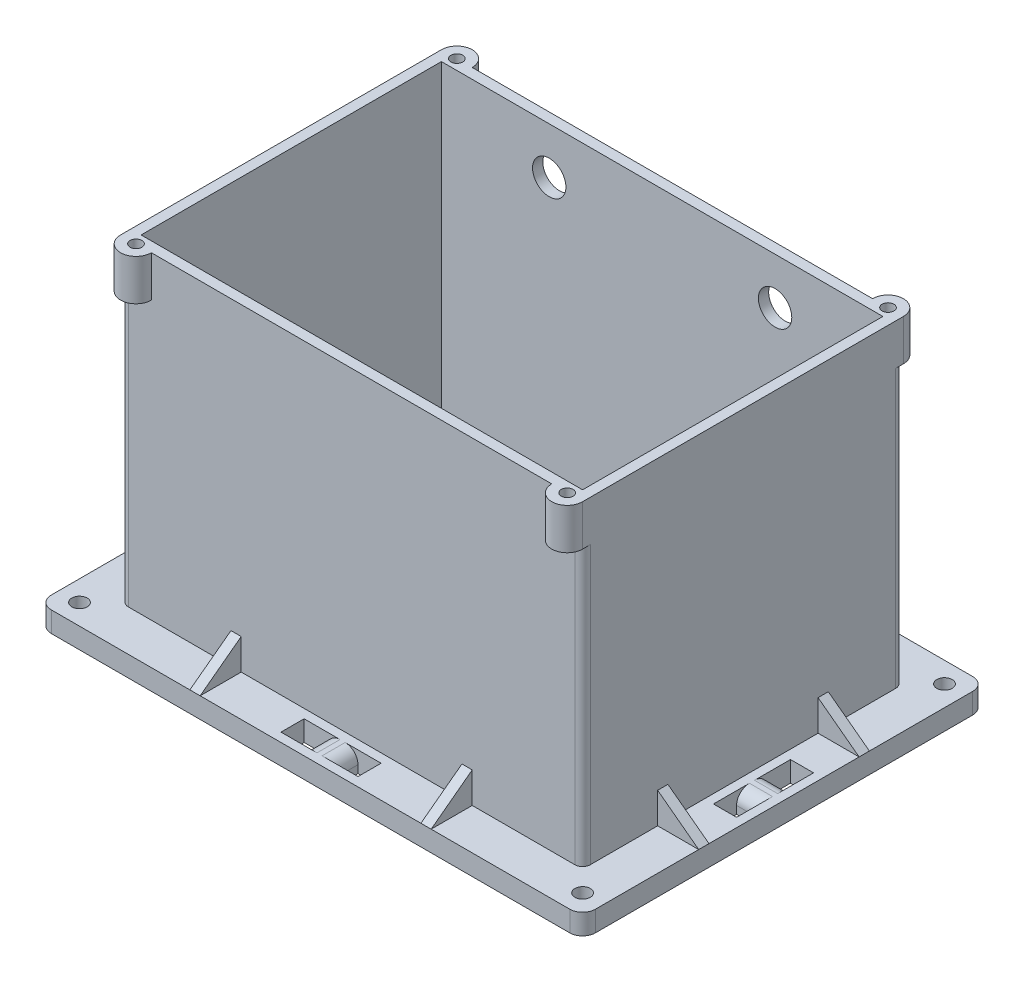
SolidWorks part; units mm, degrees
material "ABS"
ref_plane "Front Plane" through (0, 0, 0) normal (0, 0, 1) x (1, 0, 0)
ref_plane "Top Plane" through (0, 0, 0) normal (0, 1, 0) x (1, 0, 0)
ref_plane "Right Plane" through (0, 0, 0) normal (1, 0, 0) x (0, 0, -1)
sketch "Base" plane through (0, 0, 0) normal (0, 1, 0) x (1, 0, 0)
  line L1 (0, 0) -> (90, 0)
  line L2 (0, 0) -> (0, 62.5)
  line L3 (0, 62.5) -> (90, 62.5)
  line L4 (90, 0) -> (90, 62.5)
  dimension "D1" = 62.5
  dimension "D2" = 90
extrude "Base Extrude" add sketch "Base" along normal blind 2
sketch "Walls" plane through (0, 2, 0) normal (0, 1, 0) x (1, 0, 0)
  line L0 (0, 62.5) -> (0, 0) construction
  line L1 (2, 2) -> (88, 2)
  line L2 (2, 2) -> (2, 60.5)
  line L3 (2, 60.5) -> (88, 60.5)
  line L4 (88, 2) -> (88, 60.5)
  line L5 (90, 62.5) -> (0, 62.5) construction
  dimension "D1" = 86
  dimension "D2" = 58.5
  dimension "D3" = 2
  dimension "D4" = 2
extrude "Walls Extrude" add sketch "Walls" along normal blind 64 thin
sketch "Outjut" plane through (0, 66, 0) normal (0, 1, 0) x (1, 0, 0)
  line L0 (0, 0) -> (0, 62.5) construction
  line L1 (0, 62.5) -> (6, 62.5)
  line L2 (90, 62.5) -> (84, 62.5)
  line L3 (45, 64) -> (45, 0) construction
  line L4 (0, 0) -> (90, 0) construction
  line L5 (0, 31.25) -> (92, 31.25) construction
  line L6 (90, 0) -> (84, 0)
  line L7 (0, 0) -> (6, 0)
  arc A0 (0, 62.5) -> (6, 62.5) centre (3, 62.5) cw
  arc A1 (90, 62.5) -> (84, 62.5) centre (87, 62.5) ccw
  arc A2 (90, 0) -> (84, 0) centre (87, 0) cw
  arc A3 (0, 0) -> (6, 0) centre (3, 0) ccw
  point P4 (3, 65.5)
  dimension "D1" = 6
  dimension "D2" = 3
extrude "Outjut Extrude" add sketch "Outjut" against normal blind 8
sketch "Holes" plane through (0, 66, 0) normal (0, 1, 0) x (1, 0, 0)
  line L0 (45, 62.5) -> (45, 0) construction
  line L2 (84, 62.5) -> (6, 62.5) construction
  line L3 (6, 0) -> (84, 0) construction
  line L4 (90, 31.25) -> (0, 31.25) construction
  line L5 (90, 0) -> (90, 62.5) construction
  line L6 (0, 62.5) -> (0, 0) construction
  circle A1 centre (3, 62.5) radius 1.15
  circle A2 centre (87, 62.5) radius 1.15
  circle A3 centre (87, 0) radius 1.15
  circle A4 centre (3, 0) radius 1.15
  dimension "D1" = 2.3
extrude "Holes Cut" cut sketch "Holes" against normal blind 6
sketch "Switch Hole" plane through (0, 0, 0) normal (0, 0, 1) x (1, 0, 0)
  line L0 (90, 58) -> (90, 0) construction
  line L2 (0, 0) -> (90, 0) construction
  line L5 (74, 23) -> (85, 23)
  line L6 (74, 23) -> (74, 28)
  line L7 (74, 28) -> (85, 28)
  line L8 (85, 23) -> (85, 28)
  dimension "D1" = 11
  dimension "D2" = 5
  dimension "D3" = 5
  dimension "D4" = 23
extrude "Switch Hole Cut" [suppressed] cut sketch "Switch Hole" against normal up to surface (2 mm away)
sketch "Antenna/GPS Holes" plane through (0, 0, -62.5) normal (0, 0, -1) x (-1, 0, 0)
  line L0 (-90, 0) -> (0, 0) construction
  line L1 (0, 58) -> (0, 0) construction
  line L2 (-45, 66) -> (-45, 0) construction
  line L3 (-84, 66) -> (-6, 66) construction
  circle A0 centre (-23, 56.95) radius 3.25
  circle A2 centre (-67, 56.95) radius 3.25
  dimension "D1" = 6.5
  dimension "D2" = 56.95
  dimension "D3" = 23
extrude "Antenna/GPS Holes Cut" cut sketch "Antenna/GPS Holes" against normal up to surface (2 mm away) up to face at (45, 34, -60.5)
sketch "Pad" plane through (0, 0, 0) normal (0, -1, 0) x (1, 0, 0)
  line L2 (0, 0) -> (0, -62.5)
  line L4 (-8, 8) -> (-8, -70.5)
  line L5 (0, 0) -> (90, 0)
  line L7 (-8, 8) -> (98, 8)
  line L9 (90, -62.5) -> (0, -62.5)
  line L11 (98, -70.5) -> (-8, -70.5)
  line L14 (90, -62.5) -> (90, 0)
  line L16 (98, -70.5) -> (98, 8)
  dimension "D2" = 8
  dimension "D1" = 8
  dimension "D3" = 8
  dimension "D4" = 8
extrude "Pad Extrude" add sketch "Pad" against normal blind 4 contours L7 L16 L11 L4
sketch "Screw Holes" plane through (0, 4, 0) normal (0, 1, 0) x (1, 0, 0)
  line L0 (98, 70.5) -> (90, 62.5) construction
  line L1 (45, 70.5) -> (45, -8) construction
  line L2 (98, 70.5) -> (-8, 70.5) construction
  line L3 (-8, -8) -> (98, -8) construction
  line L4 (-8, 31.25) -> (98, 31.25) construction
  line L5 (-8, -8) -> (-8, 70.5) construction
  line L6 (98, 70.5) -> (98, -8) construction
  circle A0 centre (94, 66.5) radius 1.5
  circle A1 centre (-4, 66.5) radius 1.5
  circle A2 centre (94, -4) radius 1.5
  circle A3 centre (-4, -4) radius 1.5
  dimension "D1" = 3
extrude "Screw Holes Cut" cut sketch "Screw Holes" against normal through all
fillet "Wall Fillets" radius 1.5 4 edges at (90, 31, -62.5) (90, 31, 0) (0, 31, 0) (0, 31, -62.5)
ref_plane "Length Support Plane" through (22.5, 0, 0) normal (1, 0, 0) x (0, 0, -1)
ref_plane "Length Center Plane" through (45, 0, 0) normal (1, 0, 0) x (0, 0, -1)
ref_plane "Width Support Plane" through (0, 0, -15.625) normal (0, 0, 1) x (1, 0, 0)
ref_plane "Width Center Plane" through (0, 0, -31.25) normal (0, 0, 1) x (1, 0, 0)
sketch "Length Supports" plane through (22.5, 0, 0) normal (1, 0, 0) x (0, 0, -1)
  line L0 (0, 4) -> (-8, 4)
  line L1 (-8, 4) -> (0, 10)
  line L2 (0, 4) -> (0, 58) construction
  line L3 (0, 10) -> (0, 4)
  dimension "D1" = 6
extrude "Length Supports Extrude" add sketch "Length Supports" along normal blind 1 and the other way blind 1
mirror "Length Support Extrude Mirror" about plane through (45, 0, 0) normal (1, 0, 0) of "Length Supports Extrude"
mirror "Length Support Extrude Opposing Mirror" about plane through (0, 0, -31.25) normal (0, 0, 1) of "Length Supports Extrude", "Length Support Extrude Mirror"
sketch "Width Supports" plane through (0, 0, -15.625) normal (0, 0, 1) x (1, 0, 0)
  line L0 (0, 4) -> (-8, 4)
  line L1 (-8, 4) -> (0, 10)
  line L2 (0, 4) -> (0, 58) construction
  line L3 (0, 10) -> (0, 4)
  dimension "D1" = 6
extrude "Width Supports Extrude" add sketch "Width Supports" along normal blind 1 and the other way blind 1
mirror "Width Supports Extrude Mirror" about plane through (0, 0, -31.25) normal (0, 0, 1) of "Width Supports Extrude"
mirror "Width Supports Extrude Opposing Mirror" about plane through (45, 0, 0) normal (1, 0, 0) of "Width Supports Extrude Mirror", "Width Supports Extrude"
sketch "Zip Tie Hole" plane through (0, 4, 0) normal (0, 1, 0) x (1, 0, 0)
  line L0 (45, -36.3) -> (45, 36.3) construction
  line L1 (37.5, -6.25) -> (42, -6.25)
  line L2 (37.5, -6.25) -> (37.5, -1.75)
  line L3 (37.5, -1.75) -> (42, -1.75)
  line L4 (42, -6.25) -> (42, -1.75)
  line L5 (23.5, -8) -> (66.5, -8) construction
  dimension "D1" = 4.5
  dimension "D2" = 3
  dimension "D3" = 1.75
extrude "Zip Tie Hole Length Cut" cut sketch "Zip Tie Hole" against normal through all
mirror "Zip Tie Hole Length Mirror" about plane through (45, 0, 0) normal (1, 0, 0) of "Zip Tie Hole Length Cut"
mirror "Zip Tie Hole Length Opposing Mirror" about plane through (0, 0, -31.25) normal (0, 0, 1) of "Zip Tie Hole Length Mirror", "Zip Tie Hole Length Cut"
sketch "Zip Tie Hole Width" plane through (0, 4, 0) normal (0, 1, 0) x (1, 0, 0)
  line L0 (37.5, -1.75) -> (37.5, -6.25) construction
  line L1 (-6.25, 38.75) -> (-1.75, 38.75)
  line L2 (-6.25, 38.75) -> (-6.25, 34.25)
  line L3 (-6.25, 34.25) -> (-1.75, 34.25)
  line L4 (-1.75, 38.75) -> (-1.75, 34.25)
  line L5 (-8, 16.625) -> (-8, 45.875) construction
  line L6 (-36.3, 31.25) -> (36.3, 31.25) construction
  dimension "D1" = 1.75
  dimension "D2" = 3
extrude "Zip Tie Hole Width Cut" cut sketch "Zip Tie Hole Width" against normal through all
mirror "Zip Tie Hole Width Mirror" about plane through (0, 0, -31.25) normal (0, 0, 1) of "Zip Tie Hole Width Cut"
mirror "Zip Tie Hole Width Opposing Mirror" about plane through (45, 0, 0) normal (1, 0, 0) of "Zip Tie Hole Width Cut", "Zip Tie Hole Width Mirror"
fillet "Zip Tie Fillets" radius 2.5 8 edges at (48, 4, 4) (42, 4, 4) (48, 4, -66.5) (42, 4, -66.5) (94, 4, -28.25) (94, 4, -34.25) (-4, 4, -34.25) (-4, 4, -28.25)
fillet "Pad Fillets" radius 2.5 4 edges at (-8, 2, -70.5) (-8, 2, 8) (98, 2, -70.5) (98, 2, 8)
equation "\"pad\"=8"
equation "\"D2@Pad\"=\"pad\""
equation "\"D1@Pad\"=\"pad\""
equation "\"D3@Pad\"=\"pad\""
equation "\"D4@Pad\"=\"pad\""
